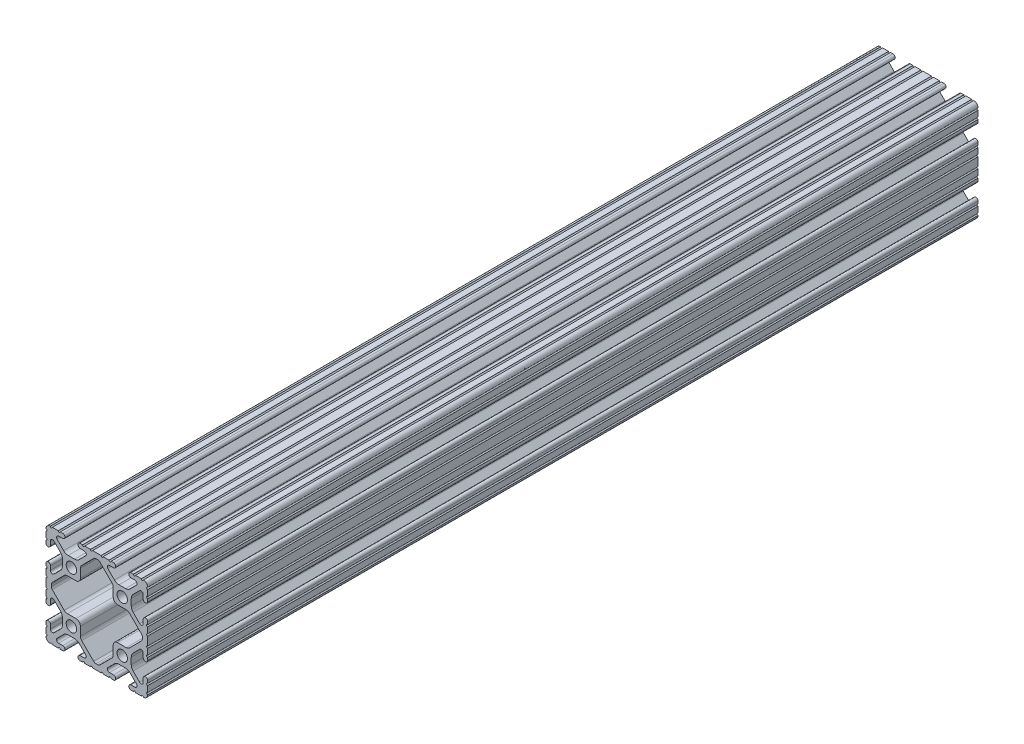
SolidWorks part; units mm, degrees
material "6061-T6 (SS)"
ref_plane "Front Plane" through (0, 0, 0) normal (0, 0, 1) x (1, 0, 0)
ref_plane "Top Plane" through (0, 0, 0) normal (0, 1, 0) x (1, 0, 0)
ref_plane "Right Plane" through (0, 0, 0) normal (1, 0, 0) x (0, 0, -1)
sketch "Sketch1" plane through (0, 0, 0) normal (0, 0, 1) x (1, 0, 0)
  line L0 (930.2944, 530.1288) -> (924.3112, 524.1455)
  line L1 (922.7486, 523.4982) -> (918.4281, 523.4982)
  line L2 (916.2183, 521.2884) -> (916.2183, 516.9678)
  line L3 (915.571, 515.4052) -> (909.5877, 509.4221)
  line L4 (908.4742, 508.9608) -> (907.5712, 508.9608)
  line L5 (906.4577, 509.422) -> (900.4743, 515.4053)
  line L6 (899.827, 516.9678) -> (899.827, 521.2884)
  line L7 (897.6172, 523.4982) -> (893.2966, 523.4982)
  line L8 (891.734, 524.1455) -> (885.7509, 530.1287)
  line L9 (885.2897, 531.2423) -> (885.2897, 532.1453)
  line L10 (885.7509, 533.2588) -> (891.7341, 539.2422)
  line L11 (893.2967, 539.8894) -> (897.6172, 539.8894)
  line L12 (899.827, 542.0992) -> (899.827, 546.4199)
  line L13 (900.4743, 547.9825) -> (906.4576, 553.9656)
  line L14 (907.5711, 554.4268) -> (908.4741, 554.4268)
  line L15 (909.5876, 553.9656) -> (915.571, 547.9824)
  line L16 (916.2183, 546.4198) -> (916.2183, 542.0992)
  line L17 (918.4281, 539.8894) -> (922.7487, 539.8894)
  line L18 (924.3113, 539.2422) -> (930.2944, 533.2589)
  line L19 (930.7557, 532.1454) -> (930.7557, 531.2424)
  line L20 (910.1563, 557.0938) -> (905.8891, 557.0938)
  line L21 (904.8731, 557.0938) -> (901.9267, 557.0938)
  line L22 (900.9107, 557.0938) -> (899.6788, 557.0938)
  line L23 (899.6788, 554.884) -> (901.7276, 554.884)
  line L24 (902.4778, 553.1122) -> (899.1939, 549.8282)
  line L25 (896.9488, 548.8982) -> (893.6964, 548.8982)
  line L26 (891.4513, 549.8282) -> (888.1676, 553.112)
  line L27 (888.9241, 554.884) -> (890.9666, 554.884)
  line L28 (890.9666, 557.0938) -> (889.7347, 557.0938)
  line L29 (888.7187, 557.0938) -> (885.7723, 557.0938)
  line L30 (884.7563, 557.0938) -> (884.7309, 557.0938)
  line L31 (882.6227, 554.9856) -> (882.6227, 554.9602)
  line L32 (882.6227, 553.9442) -> (882.6227, 550.9978)
  line L33 (882.6227, 549.9818) -> (882.6227, 548.7499)
  line L34 (884.8325, 548.7499) -> (884.8325, 550.7988)
  line L35 (886.6043, 551.549) -> (889.8883, 548.2651)
  line L36 (890.8183, 546.02) -> (890.8183, 542.7676)
  line L37 (889.8883, 540.5225) -> (886.6045, 537.2388)
  line L38 (884.8325, 537.9953) -> (884.8325, 540.0377)
  line L39 (882.6227, 540.0377) -> (882.6227, 538.8058)
  line L40 (882.6227, 537.7898) -> (882.6227, 534.8434)
  line L41 (882.6227, 533.8274) -> (882.6227, 529.5602)
  line L42 (882.6227, 528.5442) -> (882.6227, 525.5978)
  line L43 (882.6227, 524.5818) -> (882.6227, 523.3499)
  line L44 (884.8325, 523.3499) -> (884.8325, 525.3988)
  line L45 (886.6043, 526.149) -> (889.8883, 522.8651)
  line L46 (890.8183, 520.62) -> (890.8183, 517.3676)
  line L47 (889.8883, 515.1225) -> (886.6045, 511.8388)
  line L48 (884.8325, 512.5953) -> (884.8325, 514.6377)
  line L49 (882.6227, 514.6377) -> (882.6227, 513.4058)
  line L50 (882.6227, 512.3898) -> (882.6227, 509.4434)
  line L51 (882.6227, 508.4274) -> (882.6227, 508.402)
  line L52 (884.7309, 506.2938) -> (884.7563, 506.2938)
  line L53 (885.7723, 506.2938) -> (888.7187, 506.2938)
  line L54 (889.7347, 506.2938) -> (890.9666, 506.2938)
  line L55 (890.9666, 508.5036) -> (888.9177, 508.5036)
  line L56 (888.1675, 510.2755) -> (891.4514, 513.5595)
  line L57 (893.6965, 514.4894) -> (896.9489, 514.4894)
  line L58 (899.194, 513.5595) -> (902.4777, 510.2757)
  line L59 (901.7212, 508.5036) -> (899.6788, 508.5036)
  line L60 (899.6788, 506.2938) -> (900.9107, 506.2938)
  line L61 (901.9267, 506.2938) -> (904.8731, 506.2938)
  line L62 (905.8891, 506.2938) -> (910.1563, 506.2938)
  line L63 (911.1723, 506.2938) -> (914.1187, 506.2938)
  line L64 (915.1347, 506.2938) -> (916.3666, 506.2938)
  line L65 (916.3666, 508.5036) -> (914.3177, 508.5036)
  line L66 (913.5675, 510.2755) -> (916.8514, 513.5595)
  line L67 (919.0965, 514.4894) -> (922.3489, 514.4894)
  line L68 (924.594, 513.5595) -> (927.8777, 510.2757)
  line L69 (927.1212, 508.5036) -> (925.0788, 508.5036)
  line L70 (925.0788, 506.2938) -> (926.3107, 506.2938)
  line L71 (927.3267, 506.2938) -> (930.2731, 506.2938)
  line L72 (931.2891, 506.2938) -> (931.3145, 506.2938)
  line L73 (933.4227, 508.402) -> (933.4227, 508.4274)
  line L74 (933.4227, 509.4434) -> (933.4227, 512.3898)
  line L75 (933.4227, 513.4058) -> (933.4227, 514.6377)
  line L76 (931.2129, 514.6377) -> (931.2129, 512.5889)
  line L77 (929.441, 511.8386) -> (926.157, 515.1226)
  line L78 (925.227, 517.3677) -> (925.227, 520.6201)
  line L79 (926.157, 522.8652) -> (929.4408, 526.1489)
  line L80 (931.2129, 525.3923) -> (931.2129, 523.3499)
  line L81 (933.4227, 523.3499) -> (933.4227, 524.5818)
  line L82 (933.4227, 525.5978) -> (933.4227, 528.5442)
  line L83 (933.4227, 529.5602) -> (933.4227, 533.8274)
  line L84 (933.4227, 534.8434) -> (933.4227, 537.7898)
  line L85 (933.4227, 538.8058) -> (933.4227, 540.0377)
  line L86 (931.2129, 540.0377) -> (931.2129, 537.9889)
  line L87 (929.441, 537.2386) -> (926.157, 540.5226)
  line L88 (925.227, 542.7677) -> (925.227, 546.0201)
  line L89 (926.157, 548.2652) -> (929.4408, 551.5489)
  line L90 (931.2129, 550.7923) -> (931.2129, 548.7499)
  line L91 (933.4227, 548.7499) -> (933.4227, 549.9818)
  line L92 (933.4227, 550.9978) -> (933.4227, 553.9442)
  line L93 (933.4227, 554.9602) -> (933.4227, 554.9856)
  line L94 (931.3145, 557.0938) -> (931.2891, 557.0938)
  line L95 (930.2731, 557.0938) -> (927.3267, 557.0938)
  line L96 (926.3107, 557.0938) -> (925.0788, 557.0938)
  line L97 (925.0788, 554.884) -> (927.1276, 554.884)
  line L98 (927.8778, 553.1122) -> (924.5939, 549.8282)
  line L99 (922.3488, 548.8982) -> (919.0964, 548.8982)
  line L100 (916.8513, 549.8282) -> (913.5676, 553.112)
  line L101 (914.3241, 554.884) -> (916.3666, 554.884)
  line L102 (916.3666, 557.0938) -> (915.1347, 557.0938)
  line L103 (914.1187, 557.0938) -> (911.1723, 557.0938)
  arc A0 (930.2944, 530.1288) -> (930.7557, 531.2424) centre (929.1809, 531.2424) ccw
  arc A1 (922.7486, 523.4982) -> (924.3112, 524.1455) centre (922.7486, 525.708) ccw
  arc A2 (918.4281, 523.4982) -> (916.2183, 521.2884) centre (918.4281, 521.2884) ccw
  arc A3 (915.571, 515.4052) -> (916.2183, 516.9678) centre (914.0085, 516.9678) ccw
  arc A4 (908.4742, 508.9608) -> (909.5877, 509.4221) centre (908.4742, 510.5356) ccw
  arc A5 (906.4577, 509.422) -> (907.5712, 508.9608) centre (907.5712, 510.5356) ccw
  arc A6 (899.827, 516.9678) -> (900.4743, 515.4053) centre (902.0368, 516.9678) ccw
  arc A7 (899.827, 521.2884) -> (897.6172, 523.4982) centre (897.6172, 521.2884) ccw
  arc A8 (891.734, 524.1455) -> (893.2966, 523.4982) centre (893.2966, 525.708) ccw
  arc A9 (885.2897, 531.2423) -> (885.7509, 530.1287) centre (886.8645, 531.2423) ccw
  arc A10 (885.7509, 533.2588) -> (885.2897, 532.1453) centre (886.8645, 532.1453) ccw
  arc A11 (893.2967, 539.8894) -> (891.7341, 539.2422) centre (893.2967, 537.6796) ccw
  arc A12 (897.6172, 539.8894) -> (899.827, 542.0992) centre (897.6172, 542.0992) ccw
  arc A13 (900.4743, 547.9825) -> (899.827, 546.4199) centre (902.0368, 546.4199) ccw
  arc A14 (907.5711, 554.4268) -> (906.4576, 553.9656) centre (907.5711, 552.852) ccw
  arc A15 (909.5876, 553.9656) -> (908.4741, 554.4268) centre (908.4741, 552.852) ccw
  arc A16 (916.2183, 546.4198) -> (915.571, 547.9824) centre (914.0085, 546.4198) ccw
  arc A17 (916.2183, 542.0992) -> (918.4281, 539.8894) centre (918.4281, 542.0992) ccw
  arc A18 (924.3113, 539.2422) -> (922.7487, 539.8894) centre (922.7487, 537.6796) ccw
  arc A19 (930.7557, 532.1454) -> (930.2944, 533.2589) centre (929.1809, 532.1454) ccw
  circle A20 centre (920.7227, 518.9938) radius 2.6035
  circle A21 centre (895.3227, 518.9938) radius 2.6035
  circle A22 centre (920.7227, 544.3938) radius 2.6035
  circle A23 centre (895.3227, 544.3938) radius 2.6035
  arc A24 (910.1563, 557.0938) -> (911.1723, 557.0938) centre (910.6643, 557.0938) ccw
  arc A25 (904.8731, 557.0938) -> (905.8891, 557.0938) centre (905.3811, 557.0938) ccw
  arc A26 (900.9107, 557.0938) -> (901.9267, 557.0938) centre (901.4187, 557.0938) ccw
  arc A27 (899.6788, 557.0938) -> (899.6788, 554.884) centre (899.6788, 555.9889) ccw
  arc A28 (902.4778, 553.1122) -> (901.7276, 554.884) centre (901.6917, 553.8241) ccw
  arc A29 (896.9488, 548.8982) -> (899.1939, 549.8282) centre (896.9488, 552.0732) ccw
  arc A30 (891.4513, 549.8282) -> (893.6964, 548.8982) centre (893.6964, 552.0732) ccw
  arc A31 (888.9241, 554.884) -> (888.1676, 553.112) centre (888.9537, 553.8239) ccw
  arc A32 (890.9666, 554.884) -> (890.9666, 557.0938) centre (890.9666, 555.9889) ccw
  arc A33 (888.7187, 557.0938) -> (889.7347, 557.0938) centre (889.2267, 557.0938) ccw
  arc A34 (884.7563, 557.0938) -> (885.7723, 557.0938) centre (885.2643, 557.0938) ccw
  arc A35 (884.7309, 557.0938) -> (882.6227, 554.9856) centre (884.7309, 554.9856) ccw
  arc A36 (882.6227, 553.9442) -> (882.6227, 554.9602) centre (882.6227, 554.4522) ccw
  arc A37 (882.6227, 549.9818) -> (882.6227, 550.9978) centre (882.6227, 550.4898) ccw
  arc A38 (882.6227, 548.7499) -> (884.8325, 548.7499) centre (883.7276, 548.7499) ccw
  arc A39 (886.6043, 551.549) -> (884.8325, 550.7988) centre (885.8924, 550.7629) ccw
  arc A40 (890.8183, 546.02) -> (889.8883, 548.2651) centre (887.6433, 546.02) ccw
  arc A41 (889.8883, 540.5225) -> (890.8183, 542.7676) centre (887.6433, 542.7676) ccw
  arc A42 (884.8325, 537.9953) -> (886.6045, 537.2388) centre (885.8926, 538.0249) ccw
  arc A43 (884.8325, 540.0377) -> (882.6227, 540.0377) centre (883.7276, 540.0377) ccw
  arc A44 (882.6227, 537.7898) -> (882.6227, 538.8058) centre (882.6227, 538.2978) ccw
  arc A45 (882.6227, 533.8274) -> (882.6227, 534.8434) centre (882.6227, 534.3354) ccw
  arc A46 (882.6227, 528.5442) -> (882.6227, 529.5602) centre (882.6227, 529.0522) ccw
  arc A47 (882.6227, 524.5818) -> (882.6227, 525.5978) centre (882.6227, 525.0898) ccw
  arc A48 (882.6227, 523.3499) -> (884.8325, 523.3499) centre (883.7276, 523.3499) ccw
  arc A49 (886.6043, 526.149) -> (884.8325, 525.3988) centre (885.8924, 525.3629) ccw
  arc A50 (890.8183, 520.62) -> (889.8883, 522.8651) centre (887.6433, 520.62) ccw
  arc A51 (889.8883, 515.1225) -> (890.8183, 517.3676) centre (887.6433, 517.3676) ccw
  arc A52 (884.8325, 512.5953) -> (886.6045, 511.8388) centre (885.8926, 512.6249) ccw
  arc A53 (884.8325, 514.6377) -> (882.6227, 514.6377) centre (883.7276, 514.6377) ccw
  arc A54 (882.6227, 512.3898) -> (882.6227, 513.4058) centre (882.6227, 512.8978) ccw
  arc A55 (882.6227, 508.4274) -> (882.6227, 509.4434) centre (882.6227, 508.9354) ccw
  arc A56 (882.6227, 508.402) -> (884.7309, 506.2938) centre (884.7309, 508.402) ccw
  arc A57 (885.7723, 506.2938) -> (884.7563, 506.2938) centre (885.2643, 506.2938) ccw
  arc A58 (889.7347, 506.2938) -> (888.7187, 506.2938) centre (889.2267, 506.2938) ccw
  arc A59 (890.9666, 506.2938) -> (890.9666, 508.5036) centre (890.9666, 507.3987) ccw
  arc A60 (888.1675, 510.2755) -> (888.9177, 508.5036) centre (888.9536, 509.5636) ccw
  arc A61 (893.6965, 514.4894) -> (891.4514, 513.5595) centre (893.6965, 511.3144) ccw
  arc A62 (899.194, 513.5595) -> (896.9489, 514.4894) centre (896.9489, 511.3144) ccw
  arc A63 (901.7212, 508.5036) -> (902.4777, 510.2757) centre (901.6916, 509.5638) ccw
  arc A64 (899.6788, 508.5036) -> (899.6788, 506.2938) centre (899.6788, 507.3987) ccw
  arc A65 (901.9267, 506.2938) -> (900.9107, 506.2938) centre (901.4187, 506.2938) ccw
  arc A66 (905.8891, 506.2938) -> (904.8731, 506.2938) centre (905.3811, 506.2938) ccw
  arc A67 (911.1723, 506.2938) -> (910.1563, 506.2938) centre (910.6643, 506.2938) ccw
  arc A68 (915.1347, 506.2938) -> (914.1187, 506.2938) centre (914.6267, 506.2938) ccw
  arc A69 (916.3666, 506.2938) -> (916.3666, 508.5036) centre (916.3666, 507.3987) ccw
  arc A70 (913.5675, 510.2755) -> (914.3177, 508.5036) centre (914.3536, 509.5636) ccw
  arc A71 (919.0965, 514.4894) -> (916.8514, 513.5595) centre (919.0965, 511.3144) ccw
  arc A72 (924.594, 513.5595) -> (922.3489, 514.4894) centre (922.3489, 511.3144) ccw
  arc A73 (927.1212, 508.5036) -> (927.8777, 510.2757) centre (927.0916, 509.5638) ccw
  arc A74 (925.0788, 508.5036) -> (925.0788, 506.2938) centre (925.0788, 507.3987) ccw
  arc A75 (927.3267, 506.2938) -> (926.3107, 506.2938) centre (926.8187, 506.2938) ccw
  arc A76 (931.2891, 506.2938) -> (930.2731, 506.2938) centre (930.7811, 506.2938) ccw
  arc A77 (931.3145, 506.2938) -> (933.4227, 508.402) centre (931.3145, 508.402) ccw
  arc A78 (933.4227, 509.4434) -> (933.4227, 508.4274) centre (933.4227, 508.9354) ccw
  arc A79 (933.4227, 513.4058) -> (933.4227, 512.3898) centre (933.4227, 512.8978) ccw
  arc A80 (933.4227, 514.6377) -> (931.2129, 514.6377) centre (932.3178, 514.6377) ccw
  arc A81 (929.441, 511.8386) -> (931.2129, 512.5889) centre (930.1529, 512.6248) ccw
  arc A82 (925.227, 517.3677) -> (926.157, 515.1226) centre (928.402, 517.3677) ccw
  arc A83 (926.157, 522.8652) -> (925.227, 520.6201) centre (928.402, 520.6201) ccw
  arc A84 (931.2129, 525.3923) -> (929.4408, 526.1489) centre (930.1527, 525.3628) ccw
  arc A85 (931.2129, 523.3499) -> (933.4227, 523.3499) centre (932.3178, 523.3499) ccw
  arc A86 (933.4227, 525.5978) -> (933.4227, 524.5818) centre (933.4227, 525.0898) ccw
  arc A87 (933.4227, 529.5602) -> (933.4227, 528.5442) centre (933.4227, 529.0522) ccw
  arc A88 (933.4227, 534.8434) -> (933.4227, 533.8274) centre (933.4227, 534.3354) ccw
  arc A89 (933.4227, 538.8058) -> (933.4227, 537.7898) centre (933.4227, 538.2978) ccw
  arc A90 (933.4227, 540.0377) -> (931.2129, 540.0377) centre (932.3178, 540.0377) ccw
  arc A91 (929.441, 537.2386) -> (931.2129, 537.9889) centre (930.1529, 538.0248) ccw
  arc A92 (925.227, 542.7677) -> (926.157, 540.5226) centre (928.402, 542.7677) ccw
  arc A93 (926.157, 548.2652) -> (925.227, 546.0201) centre (928.402, 546.0201) ccw
  arc A94 (931.2129, 550.7923) -> (929.4408, 551.5489) centre (930.1527, 550.7628) ccw
  arc A95 (931.2129, 548.7499) -> (933.4227, 548.7499) centre (932.3178, 548.7499) ccw
  arc A96 (933.4227, 550.9978) -> (933.4227, 549.9818) centre (933.4227, 550.4898) ccw
  arc A97 (933.4227, 554.9602) -> (933.4227, 553.9442) centre (933.4227, 554.4522) ccw
  arc A98 (933.4227, 554.9856) -> (931.3145, 557.0938) centre (931.3145, 554.9856) ccw
  arc A99 (930.2731, 557.0938) -> (931.2891, 557.0938) centre (930.7811, 557.0938) ccw
  arc A100 (926.3107, 557.0938) -> (927.3267, 557.0938) centre (926.8187, 557.0938) ccw
  arc A101 (925.0788, 557.0938) -> (925.0788, 554.884) centre (925.0788, 555.9889) ccw
  arc A102 (927.8778, 553.1122) -> (927.1276, 554.884) centre (927.0917, 553.8241) ccw
  arc A103 (922.3488, 548.8982) -> (924.5939, 549.8282) centre (922.3488, 552.0732) ccw
  arc A104 (916.8513, 549.8282) -> (919.0964, 548.8982) centre (919.0964, 552.0732) ccw
  arc A105 (914.3241, 554.884) -> (913.5676, 553.112) centre (914.3537, 553.8239) ccw
  arc A106 (916.3666, 554.884) -> (916.3666, 557.0938) centre (916.3666, 555.9889) ccw
  arc A107 (914.1187, 557.0938) -> (915.1347, 557.0938) centre (914.6267, 557.0938) ccw
extrude "Extrude1" add sketch "Sketch1" against normal blind 415
